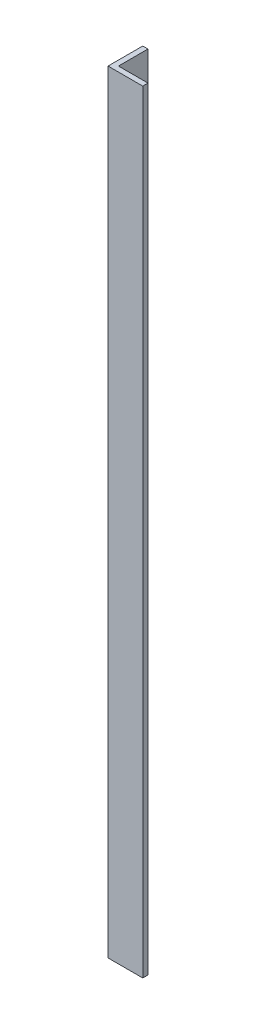
SolidWorks part; units mm, degrees
ref_plane "Front Plane" through (0, 0, 0) normal (0, 0, 1) x (1, 0, 0)
ref_plane "Top Plane" through (0, 0, 0) normal (0, 1, 0) x (1, 0, 0)
ref_plane "Right Plane" through (0, 0, 0) normal (1, 0, 0) x (0, 0, -1)
sketch "Sketch1" plane through (0, 0, 0) normal (0, 1, 0) x (1, 0, 0)
  line L2 (0, 0) -> (0, 50.8)
  line L3 (0, 50.8) -> (7.62, 50.8)
  line L4 (7.62, 7.62) -> (7.62, 50.8)
  line L5 (0, 0) -> (50.8, 0)
  line L7 (7.62, 7.62) -> (50.8, 7.62)
  line L8 (50.8, 0) -> (50.8, 7.62)
  dimension "D1" = 7.62
  dimension "D2" = 7.62
  dimension "D3" = 50.8
  dimension "D4" = 50.8
extrude "Boss-Extrude1" add sketch "Sketch1" along normal blind 1130.3
